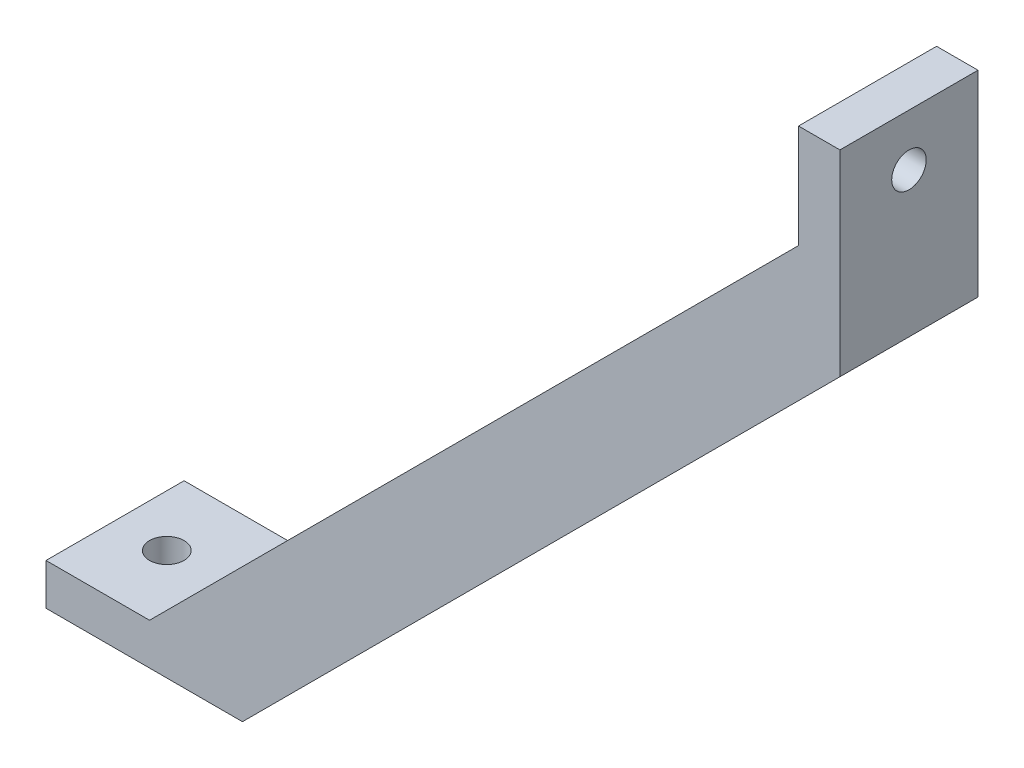
SolidWorks part; units mm, degrees
ref_plane "Front Plane" through (0, 0, 0) normal (0, 0, 1) x (1, 0, 0)
ref_plane "Top Plane" through (0, 0, 0) normal (0, 1, 0) x (1, 0, 0)
ref_plane "Right Plane" through (0, 0, 0) normal (1, 0, 0) x (0, 0, -1)
sketch "Sketch2" plane through (0, 0, 0) normal (0, 0, 1) x (1, 0, 0)
  line L2 (-115, 0) -> (-115, 6)
  line L3 (-115, 6) -> (-100, 6)
  line L4 (0, 115) -> (-6, 115)
  line L5 (-6, 115) -> (-6, 100)
  line L6 (-100, 6) -> (-6, 100)
  line L7 (-115, 0) -> (-86.5411, 0)
  line L8 (0, 115) -> (0, 86.5411)
  line L9 (-86.5411, 0) -> (0, 86.5411)
extrude "Boss-Extrude1" add sketch "Sketch2" along normal blind 20
sketch "Sketch3" plane through (-6, 0, 0) normal (-1, 0, 0) x (0, 0, 1)
  circle A0 centre (10, 107.5) radius 2.5
extrude "Cut-Extrude1" cut sketch "Sketch3" against normal blind 20
sketch "Sketch4" plane through (0, 6, 0) normal (0, 1, 0) x (1, 0, 0)
  circle A0 centre (-107.5, -10) radius 2.5
extrude "Cut-Extrude2" cut sketch "Sketch4" against normal blind 20
